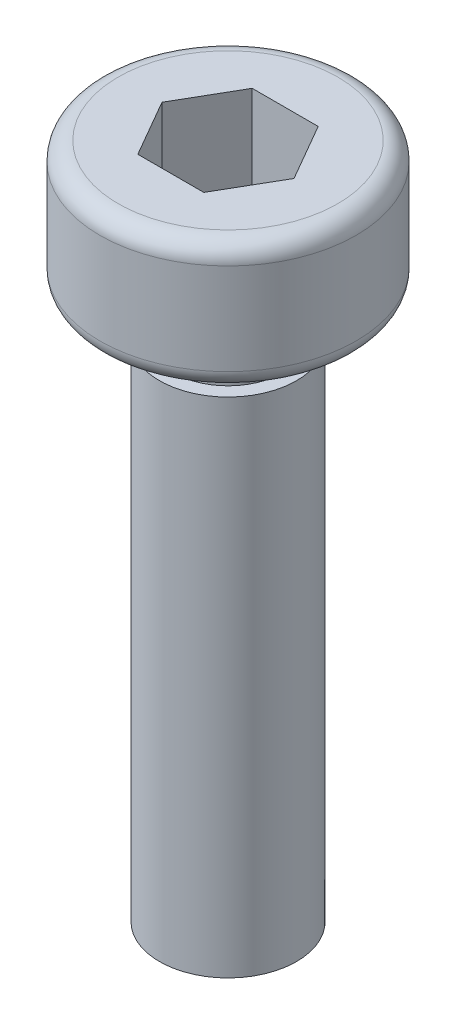
SolidWorks part; units mm, degrees
material "AISI 304"
ref_plane "前视基准面" through (0, 0, 0) normal (0, 0, 1) x (1, 0, 0)
ref_plane "上视基准面" through (0, 0, 0) normal (0, 1, 0) x (1, 0, 0)
ref_plane "右视基准面" through (0, 0, 0) normal (1, 0, 0) x (0, 0, -1)
sketch "草图1" plane through (0, 0, 0) normal (0, 0, 1) x (1, 0, 0)
  line L0 (0, 0) -> (0, 14.8) construction
  line L1 (0, 14.8) -> (-2.4, 14.8)
  line L2 (-2.8, 14.4) -> (-2.8, 12.4)
  line L3 (-2.4, 12) -> (-1.2, 12)
  line L4 (-1.2, 12) -> (-1.2, 11)
  line L5 (-1.2, 11) -> (-1.5, 11)
  line L6 (-1.5, 11) -> (-1.5, 0)
  line L7 (-1.5, 0) -> (0, 0)
  line L8 (0, 0) -> (0, 14.8)
  arc A0 (-2.8, 12.4) -> (-2.4, 12) centre (-2.4, 12.4) ccw
  arc A1 (-2.4, 14.8) -> (-2.8, 14.4) centre (-2.4, 14.4) ccw
  point P11 (-2.8, 12)
  point P14 (-2.8, 14.8)
  dimension "D7" = 0.4
  dimension "D1" = 12
  dimension "D2" = 2.8
  dimension "D3" = 5.6
  dimension "D4" = 3
  dimension "D5" = 1
  dimension "D6" = 1.2
revolve "旋转1" add sketch "草图1" angle 360 about L0
cosmetic thread "装饰螺纹线1" parameters "D2"=2.439
sketch "草图2" plane through (0, 14.8, 0) normal (0, 1, 0) x (1, 0, 0)
  line L1 (-0.7217, 1.25) -> (-1.4434, 0)
  line L2 (-1.4434, 0) -> (-0.7217, -1.25)
  line L3 (-0.7217, -1.25) -> (0.7217, -1.25)
  line L4 (0.7217, -1.25) -> (1.4434, 0)
  line L5 (1.4434, 0) -> (0.7217, 1.25)
  line L6 (0.7217, 1.25) -> (-0.7217, 1.25)
  circle A0 centre (0, 0) radius 1.25 construction
  dimension "D1" = 2.5
extrude "切除-拉伸1" cut sketch "草图2" against normal blind 2
